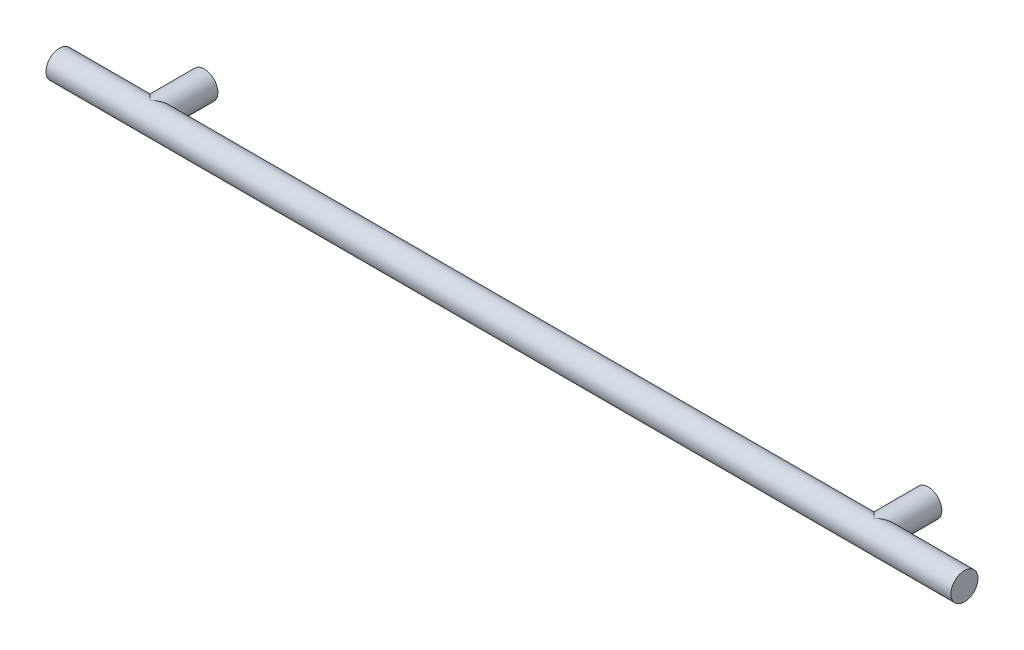
SolidWorks part; units mm, degrees
material "1023 Carbon Steel Sheet (SS)"
ref_plane "Front Plane" through (0, 0, 0) normal (0, 0, 1) x (1, 0, 0)
ref_plane "Top Plane" through (0, 0, 0) normal (0, 1, 0) x (1, 0, 0)
ref_plane "Right Plane" through (0, 0, 0) normal (1, 0, 0) x (0, 0, -1)
sketch "Sketch1" plane through (0, 0, 0) normal (0, 0, 1) x (1, 0, 0)
  line L0 (0, 0) -> (0, 50.1523) construction
  circle A0 centre (-127, 0) radius 4.7625
  circle A1 centre (127, 0) radius 4.7625
  dimension "D1" = 9.525
  dimension "D2" = 127
sketch "Sketch2" plane through (0, 0, 0) normal (1, 0, 0) x (0, 0, -1)
  circle A0 centre (-19.05, 0) radius 4.7625
  point P2 (0, 0)
  dimension "D1" = 9.525
  dimension "D2" = 19.05
extrude "Boss-Extrude1" add sketch "Sketch2" along normal mid plane 317.5
extrude "Boss-Extrude2" add sketch "Sketch1" along normal up to next
sketch "Sketch3" plane through (158.75, 0, 0) normal (1, 0, 0) x (0, 0, -1)
  line L1 (-23.8125, 0) -> (-14.2875, 0)
  circle A1 centre (-19.05, 0) radius 4.7625 construction
  arc A2 (-19.05, -4.7625) -> (-19.05, 4.7625) centre (-19.05, 0) ccw construction
